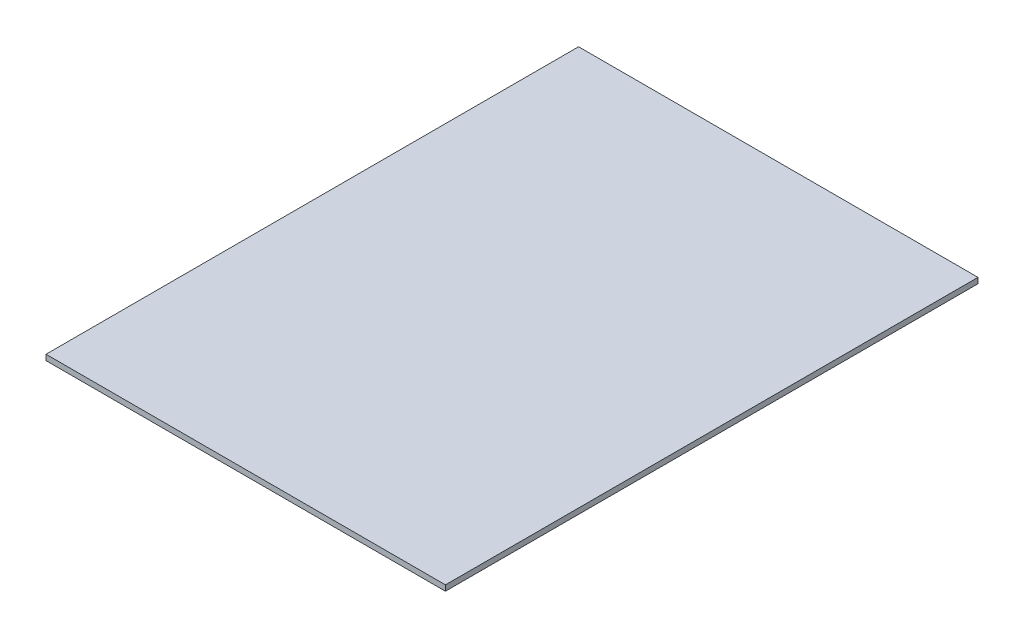
SolidWorks part; units mm, degrees
ref_plane "Front Plane" through (0, 0, 0) normal (0, 0, 1) x (1, 0, 0)
ref_plane "Top Plane" through (0, 0, 0) normal (0, 1, 0) x (1, 0, 0)
ref_plane "Right Plane" through (0, 0, 0) normal (1, 0, 0) x (0, 0, -1)
sketch "Sketch1" plane through (0, 0, 0) normal (0, 1, 0) x (1, 0, 0)
  line L1 (-228.4076, -183.4149) -> (228.7924, -183.4149)
  line L2 (-228.4076, -183.4149) -> (-228.4076, -793.0149)
  line L3 (-228.4076, -793.0149) -> (228.7924, -793.0149)
  line L4 (228.7924, -183.4149) -> (228.7924, -793.0149)
  dimension "D1" = 457.2
  dimension "D2" = 609.6
extrude "Boss-Extrude1" add sketch "Sketch1" against normal blind 6.35 contours L1 L4 L3 L2
